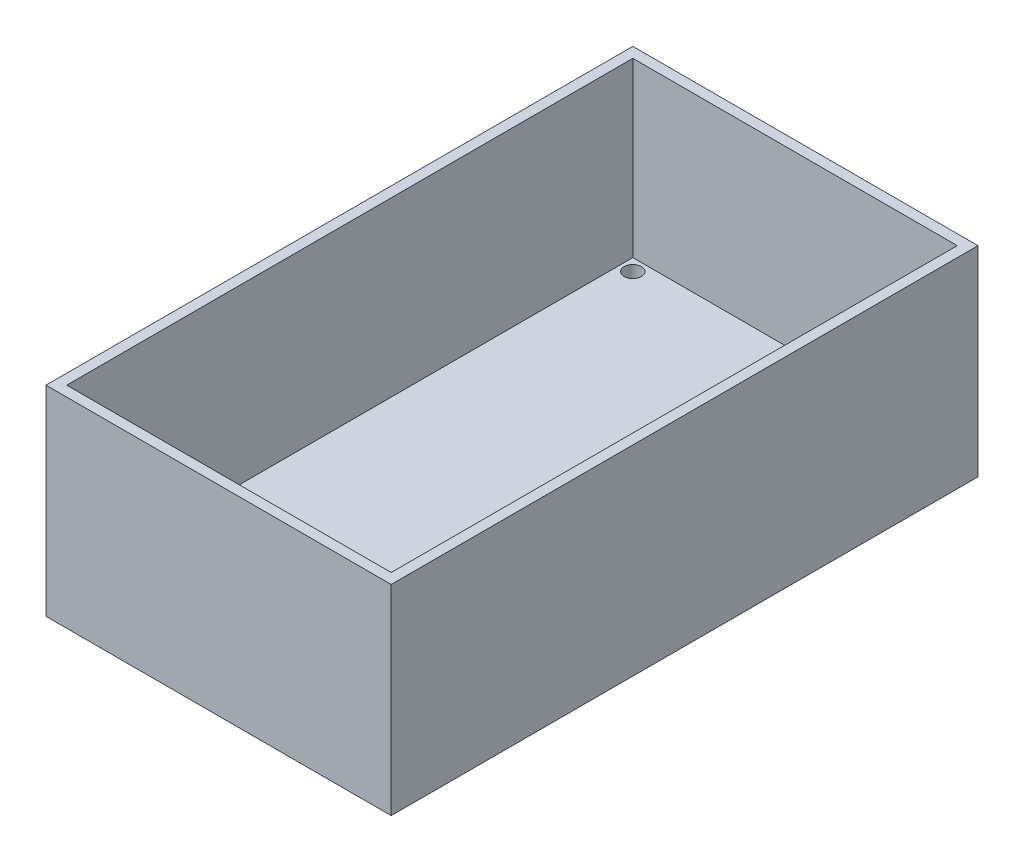
SolidWorks part; units mm, degrees
ref_plane "Front Plane" through (0, 0, 0) normal (0, 0, 1) x (1, 0, 0)
ref_plane "Top Plane" through (0, 0, 0) normal (0, 1, 0) x (1, 0, 0)
ref_plane "Right Plane" through (0, 0, 0) normal (1, 0, 0) x (0, 0, -1)
sketch "Sketch1" plane through (0, 0, 0) normal (0, 1, 0) x (1, 0, 0)
  line L0 (46, 40.5) -> (-5.6417, 40.5) construction
  line L1 (0, 0) -> (46, 0)
  line L2 (0, 0) -> (0, 81)
  line L3 (0, 81) -> (46, 81)
  line L4 (46, 0) -> (46, 81)
  line L5 (-2, -2) -> (-2, 83)
  line L6 (-2, 83) -> (48, 83)
  line L7 (48, -2) -> (48, 83)
  line L8 (-2, -2) -> (48, -2)
  circle A0 centre (1.25, 79.75) radius 1.25
  circle A1 centre (44.75, 79.75) radius 1.25
  circle A2 centre (44.75, 1.25) radius 1.25
  circle A3 centre (1.25, 1.25) radius 1.25
  dimension "D3" = 2.5
  dimension "D4" = 2.5
  dimension "D5" = 2
  dimension "D1" = 81
  dimension "D2" = 46
extrude "Boss-Extrude3" add sketch "Sketch1" along normal blind 4
sketch "Sketch2" plane through (0, 4, 0) normal (0, 1, 0) x (1, 0, 0)
  line L0 (-0.5, 81.5) -> (-0.5, -0.5)
  line L1 (-2, 83) -> (48, 83)
  line L2 (-2, 83) -> (-2, -2)
  line L3 (-2, -2) -> (48, -2)
  line L4 (48, 83) -> (48, -2)
  line L5 (-0.5, -0.5) -> (46.5, -0.5)
  line L6 (46.5, 81.5) -> (46.5, -0.5)
  line L7 (-0.5, 81.5) -> (46.5, 81.5)
  dimension "D1" = 1.5
extrude "Boss-Extrude4" add sketch "Sketch2" along normal blind 25
